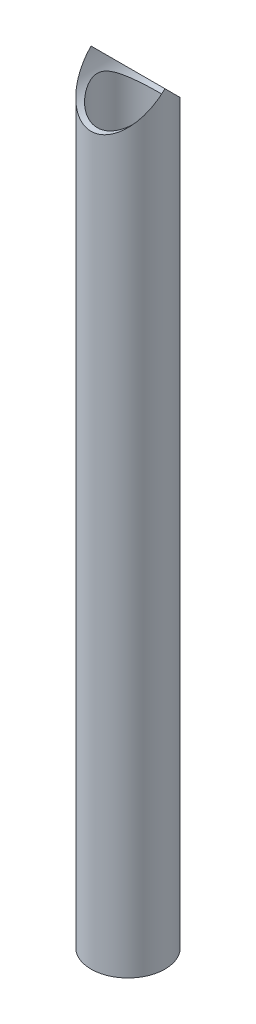
SolidWorks part; units mm, degrees
material "6061-T6 (SS)"
ref_plane "Front Plane" through (0, 0, 0) normal (0, 0, 1) x (1, 0, 0)
ref_plane "Top Plane" through (0, 0, 0) normal (0, 1, 0) x (1, 0, 0)
ref_plane "Right Plane" through (0, 0, 0) normal (1, 0, 0) x (0, 0, -1)
sketch "Sketch1" plane through (0, 0, 0) normal (0, 1, 0) x (1, 0, 0)
  circle A0 centre (0, 0) radius 21.082
  circle A1 centre (0, 0) radius 17.526
  dimension "D1" = 42.164
  dimension "D2" = 35.052
extrude "Boss-Extrude1" add sketch "Sketch1" along normal blind 434.975
sketch "Sketch2" plane through (0, 0, 0) normal (0, 0, 1) x (1, 0, 0)
  line L0 (21.082, 434.975) -> (-21.082, 434.975) construction
  circle A1 centre (0, 434.975) radius 21.082
  dimension "D1" = 42.164
extrude "Cut-Extrude1" cut sketch "Sketch2" against normal through all both and the other way through all
